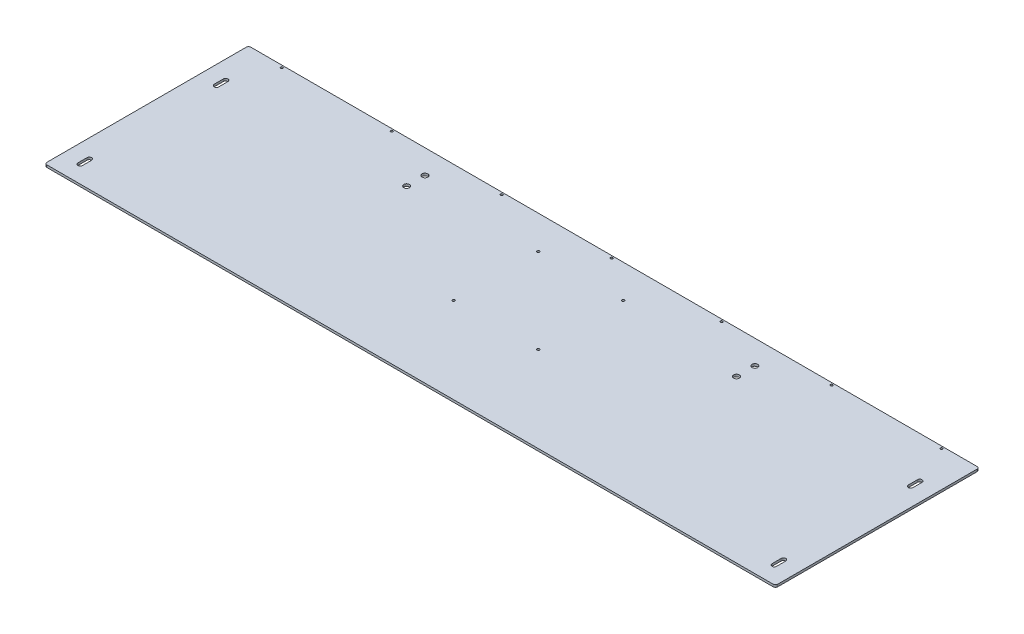
SolidWorks part; units mm, degrees
material "PC High Viscosity"
ref_plane "Front Plane" through (0, 0, 0) normal (0, 0, 1) x (1, 0, 0)
ref_plane "Top Plane" through (0, 0, 0) normal (0, 1, 0) x (1, 0, 0)
ref_plane "Right Plane" through (0, 0, 0) normal (1, 0, 0) x (0, 0, -1)
sketch "Sketch1" plane through (0, 0, 0) normal (0, 1, 0) x (1, 0, 0)
  line L0 (555.625, 447.675) -> (1470.025, 447.675) construction
  line L1 (6.35, 0) -> (2019.3, 0)
  line L2 (0, 6.35) -> (0, 558.8)
  line L3 (6.35, 565.15) -> (2019.3, 565.15)
  line L4 (2025.65, 6.35) -> (2025.65, 558.8)
  line L5 (50.8, 73.025) -> (50.8, 47.625) construction
  line L6 (895.35, 473.075) -> (1130.3, 473.075) construction
  line L7 (895.35, 473.075) -> (895.35, 238.125) construction
  line L8 (1012.825, 565.15) -> (1012.825, 0) construction
  line L9 (57.15, 73.025) -> (57.15, 47.625)
  line L10 (44.45, 73.025) -> (44.45, 47.625)
  line L11 (1974.85, 73.025) -> (1974.85, 47.625) construction
  line L12 (1968.5, 73.025) -> (1968.5, 47.625)
  line L13 (1981.2, 73.025) -> (1981.2, 47.625)
  line L14 (555.625, 447.675) -> (555.625, 498.475) construction
  line L15 (50.8, 425.45) -> (50.8, 450.85) construction
  line L16 (44.45, 425.45) -> (44.45, 450.85)
  line L17 (57.15, 425.45) -> (57.15, 450.85)
  line L18 (1974.85, 425.45) -> (1974.85, 450.85) construction
  line L19 (1981.2, 425.45) -> (1981.2, 450.85)
  line L20 (1968.5, 425.45) -> (1968.5, 450.85)
  arc A0 (2019.3, 565.15) -> (2025.65, 558.8) centre (2019.3, 558.8) cw
  arc A1 (2019.3, 0) -> (2025.65, 6.35) centre (2019.3, 6.35) ccw
  arc A2 (6.35, 0) -> (0, 6.35) centre (6.35, 6.35) cw
  arc A3 (0, 558.8) -> (6.35, 565.15) centre (6.35, 558.8) cw
  circle A4 centre (555.625, 447.675) radius 7.9375
  circle A8 centre (1470.025, 447.675) radius 7.9375
  circle A17 centre (895.35, 473.075) radius 3.3782
  circle A18 centre (1130.3, 473.075) radius 3.3782
  circle A19 centre (1130.3, 238.125) radius 3.3782
  circle A20 centre (895.35, 238.125) radius 3.3782
  circle A23 centre (1470.025, 15.875) radius 7.9375 [skipped]
  circle A24 centre (555.625, 498.475) radius 7.9375
  arc A25 (57.15, 73.025) -> (44.45, 73.025) centre (50.8, 73.025) ccw
  circle A32 centre (555.625, 15.875) radius 7.9375 [skipped]
  arc A33 (44.45, 47.625) -> (57.15, 47.625) centre (50.8, 47.625) ccw
  arc A34 (1968.5, 73.025) -> (1981.2, 73.025) centre (1974.85, 73.025) cw
  arc A35 (1981.2, 47.625) -> (1968.5, 47.625) centre (1974.85, 47.625) cw
  circle A36 centre (1470.025, 498.475) radius 7.9375
  circle A52 centre (1012.825, 558.8) radius 3.175
  circle A53 centre (1317.625, 558.8) radius 3.175
  circle A54 centre (1622.425, 558.8) radius 3.175
  circle A55 centre (1927.225, 558.8) radius 3.175
  circle A56 centre (1012.825, 558.8) radius 3.175
  circle A57 centre (1317.625, 558.8) radius 3.175
  circle A58 centre (1622.425, 558.8) radius 3.175
  circle A59 centre (708.025, 558.8) radius 3.175
  circle A60 centre (1012.825, 558.8) radius 3.175
  circle A61 centre (1317.625, 558.8) radius 3.175
  circle A62 centre (403.225, 558.8) radius 3.175
  circle A63 centre (708.025, 558.8) radius 3.175
  circle A64 centre (1012.825, 558.8) radius 3.175
  circle A65 centre (708.025, 558.8) radius 3.175
  circle A66 centre (403.225, 558.8) radius 3.175
  circle A67 centre (98.425, 558.8) radius 3.175
  arc A68 (44.45, 425.45) -> (57.15, 425.45) centre (50.8, 425.45) ccw
  arc A69 (57.15, 450.85) -> (44.45, 450.85) centre (50.8, 450.85) ccw
  arc A70 (1981.2, 425.45) -> (1968.5, 425.45) centre (1974.85, 425.45) cw
  arc A71 (1968.5, 450.85) -> (1981.2, 450.85) centre (1974.85, 450.85) cw
  point P7 (2025.65, 565.15)
  point P12 (0, 0)
  point P15 (0, 565.15)
  point P26 (50.8, 60.325)
  point P28 (1012.825, 473.075)
  point P30 (1012.825, 447.675)
  point P58 (1974.85, 60.325)
  point P61 (50.8, 438.15)
  point P109 (1974.85, 438.15)
  dimension "D3" = 6.35
  dimension "D6" = 15.875
  dimension "D12" = 92.075
  dimension "D13" = 6.7564
  dimension "D19" = 234.95
  dimension "D20" = 6.35
  dimension "D22" = 4
  dimension "D11" = 6.35
  dimension "D25" = 2
  dimension "D1" = 2025.65
  dimension "D2" = 565.15
  dimension "D4" = 117.475
  dimension "D9" = 50.8
  dimension "D10" = 914.4
  dimension "D17" = 90
  dimension "D18" = 234.95
  dimension "D21" = 6.35
  dimension "D23" = 25.4
  dimension "D24" = 60.325
  dimension "D26" = 50.8
  dimension "D27" = 4
  dimension "D28" = 304.8
  dimension "D29" = 304.8
  dimension "D30" = 127
  dimension "D7" = 2
  dimension "D8" = 2
  dimension "D15" = 2
  dimension "D16" = 2
extrude "Boss-Extrude1" add sketch "Sketch1" along normal blind 6.35
